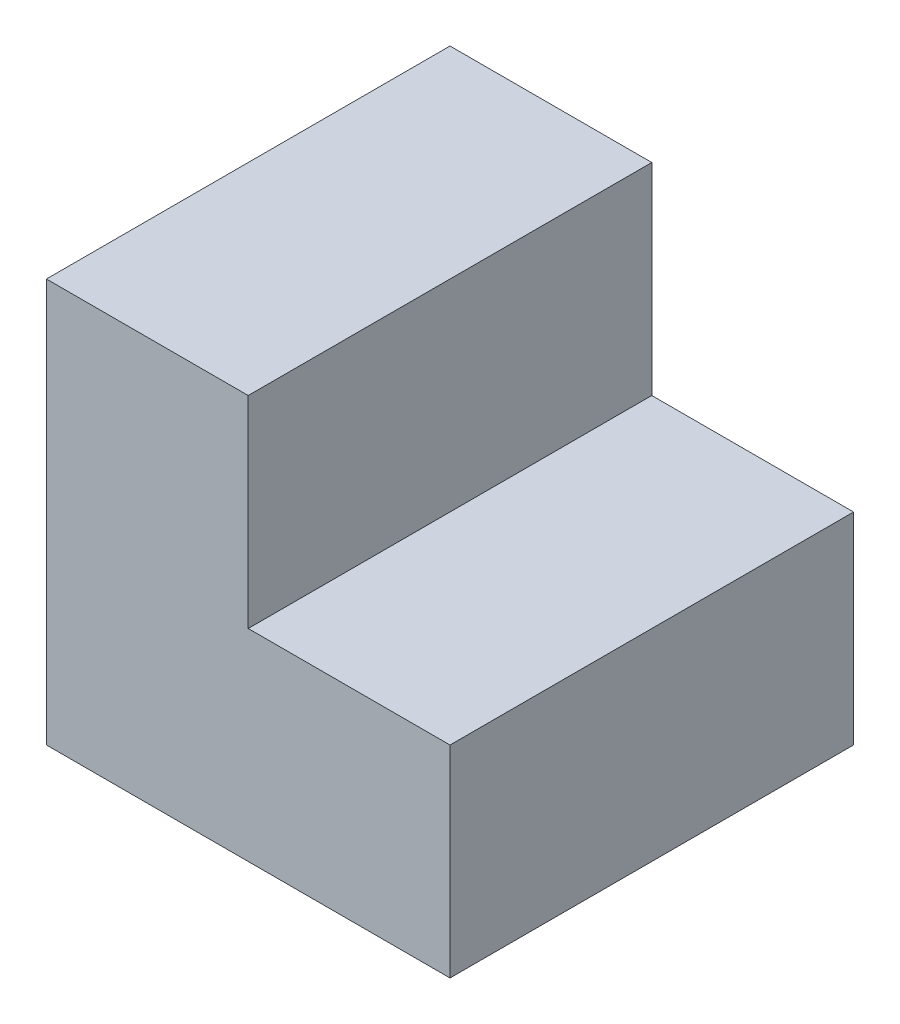
SolidWorks part; units mm, degrees
ref_plane "Front Plane" through (0, 0, 0) normal (0, 0, 1) x (1, 0, 0)
ref_plane "Top Plane" through (0, 0, 0) normal (0, 1, 0) x (1, 0, 0)
ref_plane "Right Plane" through (0, 0, 0) normal (1, 0, 0) x (0, 0, -1)
sketch "Sketch1" plane through (0, 0, 0) normal (0, 0, 1) x (1, 0, 0)
  line L1 (0, 0) -> (80, 0)
  line L2 (80, 0) -> (80, 40)
  line L3 (80, 40) -> (40, 40)
  line L4 (40, 40) -> (40, 80)
  line L5 (40, 80) -> (0, 80)
  line L7 (0, 80) -> (0, 0)
  dimension "D1" = 40
  dimension "D2" = 40
  dimension "D3" = 80
  dimension "D4" = 80
  dimension "D5" = 0
extrude "Boss-Extrude2" add sketch "Sketch1" against normal blind 80 contours L4 L5 L7 L1 L2 L3
